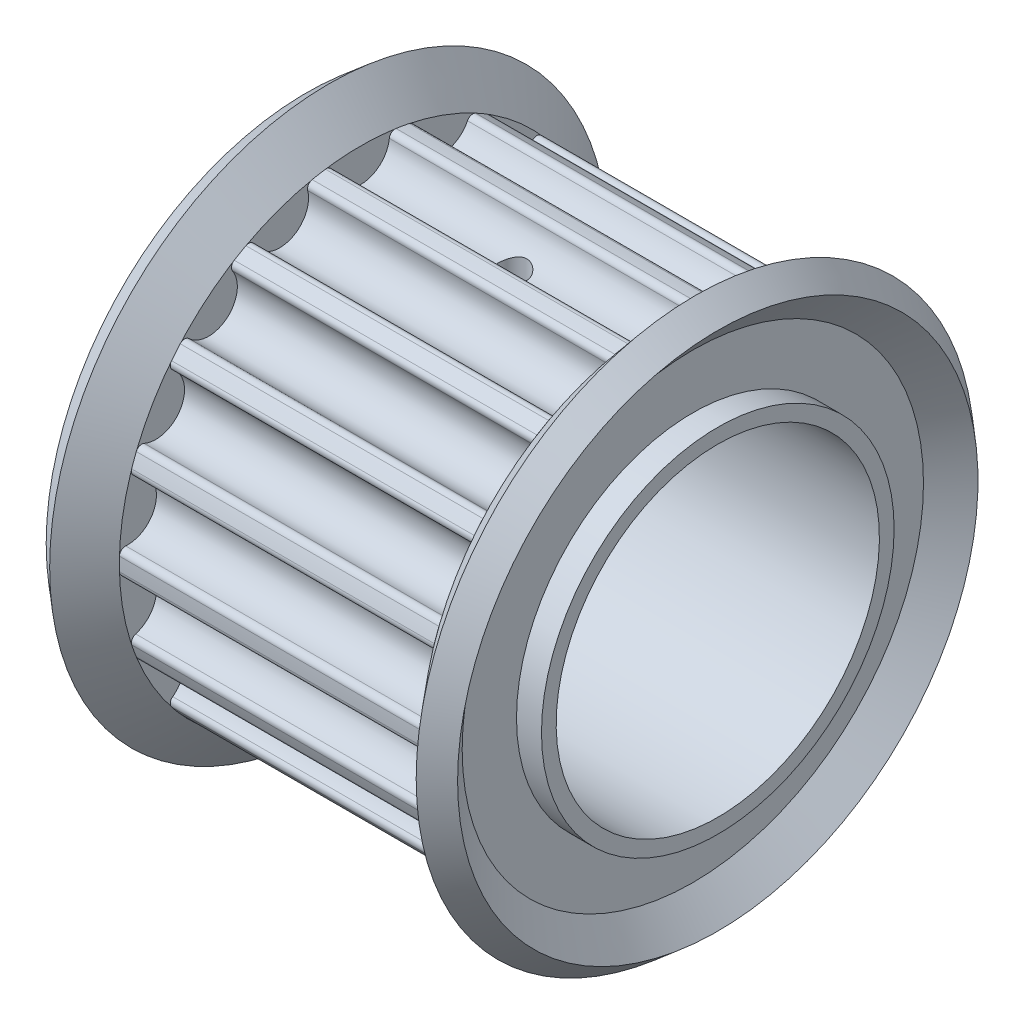
SolidWorks part; units mm, degrees
material "2014-T6"
ref_plane "Front Plane" through (0, 0, 0) normal (0, 0, 1) x (1, 0, 0)
ref_plane "Top Plane" through (0, 0, 0) normal (0, 1, 0) x (1, 0, 0)
ref_plane "Right Plane" through (0, 0, 0) normal (1, 0, 0) x (0, 0, -1)
sketch "Sketch1" plane through (0, 0, 0) normal (0, 0, 1) x (1, 0, 0)
  line L0 (-7, 4) -> (7, 4)
  line L1 (7, 4) -> (7, 6)
  line L2 (7, 6) -> (5.15, 6)
  line L3 (5.15, 6) -> (5.15, 8.215)
  line L4 (5.15, 8.215) -> (-5.15, 8.215)
  line L5 (-5.15, 8.215) -> (-5.15, 6)
  line L6 (-5.15, 6) -> (-7, 6)
  line L7 (-7, 6) -> (-7, 4)
  line L8 (0, 0) -> (0, 68.2564) construction
  line L9 (-16.0415, 0) -> (16.0415, 0) construction
  line L10 (-5.15, 8.595) -> (5.15, 8.595) construction
  dimension "D1" = 16.43
  dimension "D2" = 8
  dimension "D3" = 14
  dimension "D4" = 10.3
  dimension "D5" = 17.19
  dimension "D6" = 12
revolve "Revolve1" add sketch "Sketch1" angle 360 about L9
sketch "Sketch2" plane through (0, 0, 0) normal (1, 0, 0) x (0, 0, -1)
  line L0 (0, 7.075) -> (0, 8.215) construction
  line L1 (0, 8.215) -> (0, 8.595) construction
  line L3 (0, 0) -> (0, 68.2564) construction
  line L4 (1.2, 8.1269) -> (-1.2, 8.1269) construction
  circle A0 centre (0, 0) radius 8.595 construction
  arc A1 (1.2, 8.1269) -> (-1.2, 8.1269) centre (0, 0) ccw
  circle A2 centre (0, 0) radius 8.215 construction
  circle A3 centre (0, 0) radius 7.075 construction
  arc A4 (-0.9719, 7.95) -> (0.9719, 7.95) centre (0, 8.0523) ccw
  arc A5 (-1.2, 8.1269) -> (-0.9719, 7.95) centre (-1.1708, 7.929) cw
  arc A6 (1.2, 8.1269) -> (0.9719, 7.95) centre (1.1708, 7.929) ccw
  dimension "D2" = 0.2
  dimension "D1" = 1.14
  dimension "D3" = 2.4
extrude "Cut-Extrude1" cut sketch "Sketch2" against normal through all and the other way through all
pattern_circular "CirPattern1" count 18 over 360 about axis through (0, 0, 0) along (1, 0, 0) of "Cut-Extrude1"
sketch "Sketch3" plane through (0, 0, 0) normal (0, 0, 1) x (1, 0, 0)
  line L0 (5.15, 6) -> (6.15, 6)
  line L1 (5.15, 6) -> (5.15, 8.215)
  line L2 (5.15, 8.215) -> (6.2363, 9.5)
  line L3 (6.2363, 9.5) -> (7, 8.8544)
  line L4 (7, 8.8544) -> (6.15, 7.8489)
  line L5 (6.15, 7.8489) -> (6.15, 6)
  line L6 (0, 0) -> (16.0415, 0) construction
  line L7 (0, 0) -> (0, 11.7154) construction
  line L8 (0, 0) -> (0, 68.2564) construction
  line L9 (-5.15, 6) -> (-5.15, 8.215)
  line L10 (-5.15, 6) -> (-6.15, 6)
  line L11 (-6.15, 7.8489) -> (-6.15, 6)
  line L12 (-7, 8.8544) -> (-6.15, 7.8489)
  line L13 (-6.2363, 9.5) -> (-7, 8.8544)
  line L14 (-5.15, 8.215) -> (-6.2363, 9.5)
  dimension "D1" = 1.85
  dimension "D2" = 19
  dimension "D3" = 1
revolve "Revolve2" add sketch "Sketch3" angle 360 about L6
sketch "Sketch4" plane through (0, 0, 0) normal (0, 0, 1) x (1, 0, 0)
  line L0 (0, 0) -> (-15.4218, 0) construction
  line L1 (-7, 5.5) -> (7, 5.5)
  line L2 (-7, 5.5) -> (-7, 0)
  line L3 (-7, 0) -> (7, 0)
  line L4 (7, 5.5) -> (7, 0)
  line L5 (7, -4) -> (7, 4) construction
  line L6 (-7, 4) -> (-7, -4) construction
  dimension "D1" = 11
revolve "Cut-Revolve1" cut sketch "Sketch4" angle 360 about L0
sketch "Sketch5" plane through (0, 0, 0) normal (0, 1, 0) x (1, 0, 0)
  circle A0 centre (0, 0) radius 0.5
  dimension "D1" = 1
extrude "Cut-Extrude2" cut sketch "Sketch5" along normal through all
